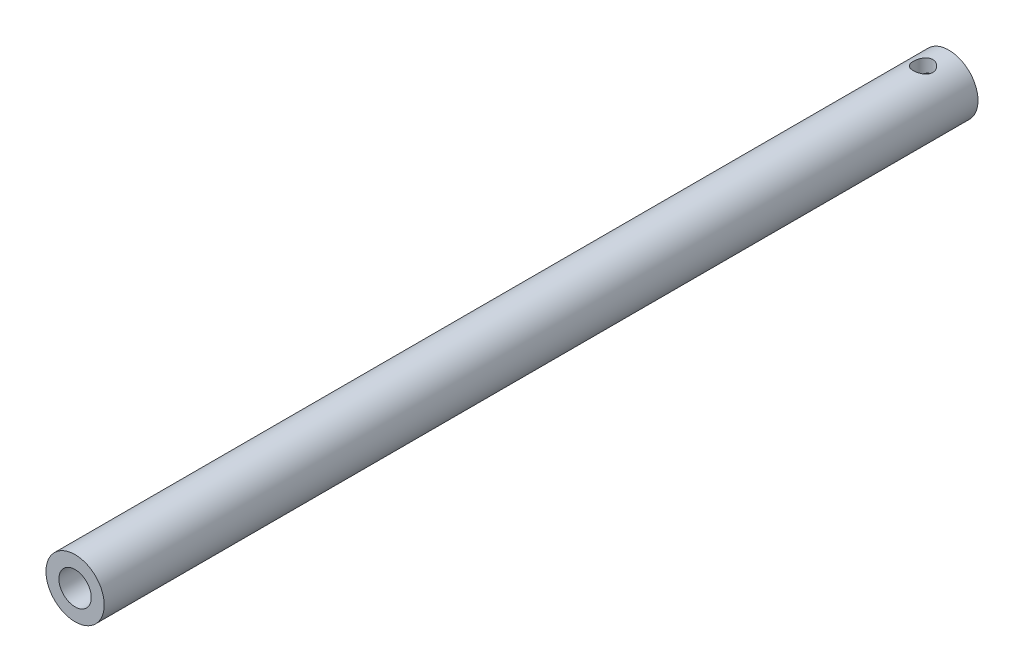
SolidWorks part; units mm, degrees
ref_plane "Front Plane" through (0, 0, 0) normal (0, 0, 1) x (1, 0, 0)
ref_plane "Top Plane" through (0, 0, 0) normal (0, 1, 0) x (1, 0, 0)
ref_plane "Right Plane" through (0, 0, 0) normal (1, 0, 0) x (0, 0, -1)
sketch "Sketch1" plane through (0, 0, 0) normal (0, 0, 1) x (1, 0, 0)
  circle A0 centre (0, 0) radius 9
  circle A1 centre (0, 0) radius 5
  dimension "D1" = 18
  dimension "D2" = 10
extrude "Boss-Extrude1" add sketch "Sketch1" along normal blind 270
sketch "Sketch2" plane through (0, 0, 0) normal (0, 1, 0) x (1, 0, 0)
  circle A0 centre (0, -8) radius 3
  dimension "D1" = 6
  dimension "D2" = 8
extrude "Cut-Extrude1" cut sketch "Sketch2" against normal through all and the other way through all
